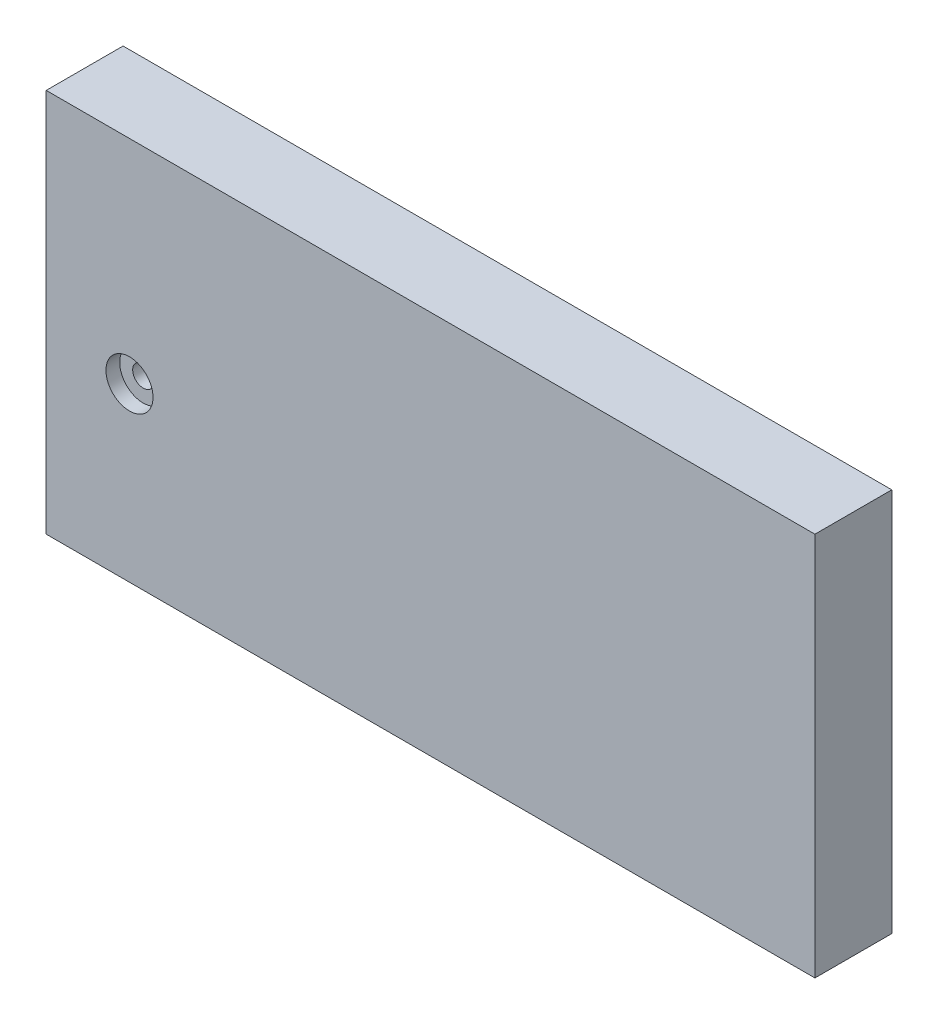
SolidWorks part; units mm, degrees
ref_plane "Front Plane" through (0, 0, 0) normal (0, 0, 1) x (1, 0, 0)
ref_plane "Top Plane" through (0, 0, 0) normal (0, 1, 0) x (1, 0, 0)
ref_plane "Right Plane" through (0, 0, 0) normal (1, 0, 0) x (0, 0, -1)
sketch "Sketch1" plane through (0, 0, 0) normal (0, 0, 1) x (1, 0, 0)
  line L1 (0, 0) -> (200, 0)
  line L2 (0, 0) -> (0, 100)
  line L3 (0, 100) -> (200, 100)
  line L4 (200, 0) -> (200, 100)
  dimension "D1" = 200
  dimension "D2" = 100
extrude "Boss-Extrude1" add sketch "Sketch1" along normal blind 20
hole_wizard "CBORE for M5 Hex Head Bolt1" positions "Sketch4" profile "Sketch3" counterbore size "M5" standard "ANSI Metric" end condition through all
sketch "Sketch4" plane through (0, 0, 20) normal (0, 0, 1) x (1, 0, 0)
  point P0 (21.6629, 44.704)
sketch "Sketch3" plane through (21.6629, 44.704, 20) normal (1, 0, 0) x (0, -1, 0)
  line L0 (0, 0) -> (0, 20)
  line L1 (0, 20) -> (2.75, 20)
  line L3 (2.75, 20) -> (2.75, 3.58)
  line L4 (2.75, 3.58) -> (6.12, 3.58)
  line L5 (6.12, 3.58) -> (6.12, 0)
  line L7 (6.12, 0) -> (0, 0)
  line L11 (0, -6.35) -> (0, 107.95) construction
  dimension "Thru Hole Dia." = 5.5
  dimension "Thru Hole Depth" = 20
  dimension "C'Bore Dia." = 12.24
  dimension "C'Bore Depth" = 3.58
